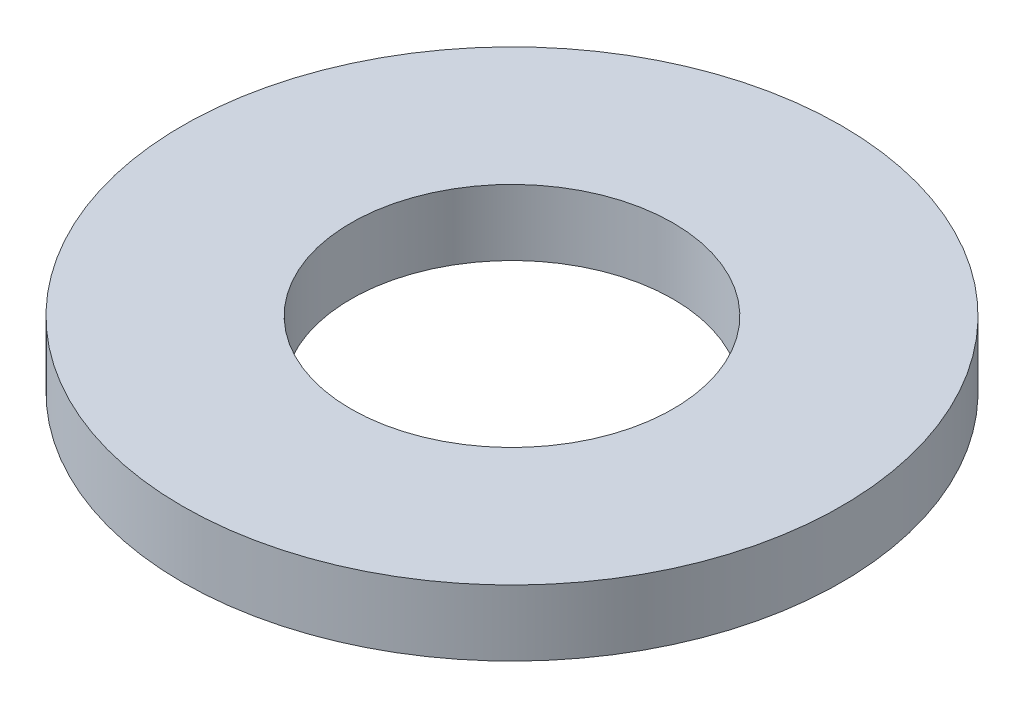
SolidWorks part; units mm, degrees
ref_plane "Front Plane" through (0, 0, 0) normal (0, 0, 1) x (1, 0, 0)
ref_plane "Top Plane" through (0, 0, 0) normal (0, 1, 0) x (1, 0, 0)
ref_plane "Right Plane" through (0, 0, 0) normal (1, 0, 0) x (0, 0, -1)
sketch "Sketch1" plane through (0, 0, 0) normal (0, 1, 0) x (1, 0, 0)
  circle A0 centre (0, 0) radius 2.2
  circle A1 centre (0, 0) radius 4.5
  dimension "D1" = 4.4
  dimension "D2" = 9
extrude "Boss-Extrude1" add sketch "Sketch1" along normal blind 0.9
